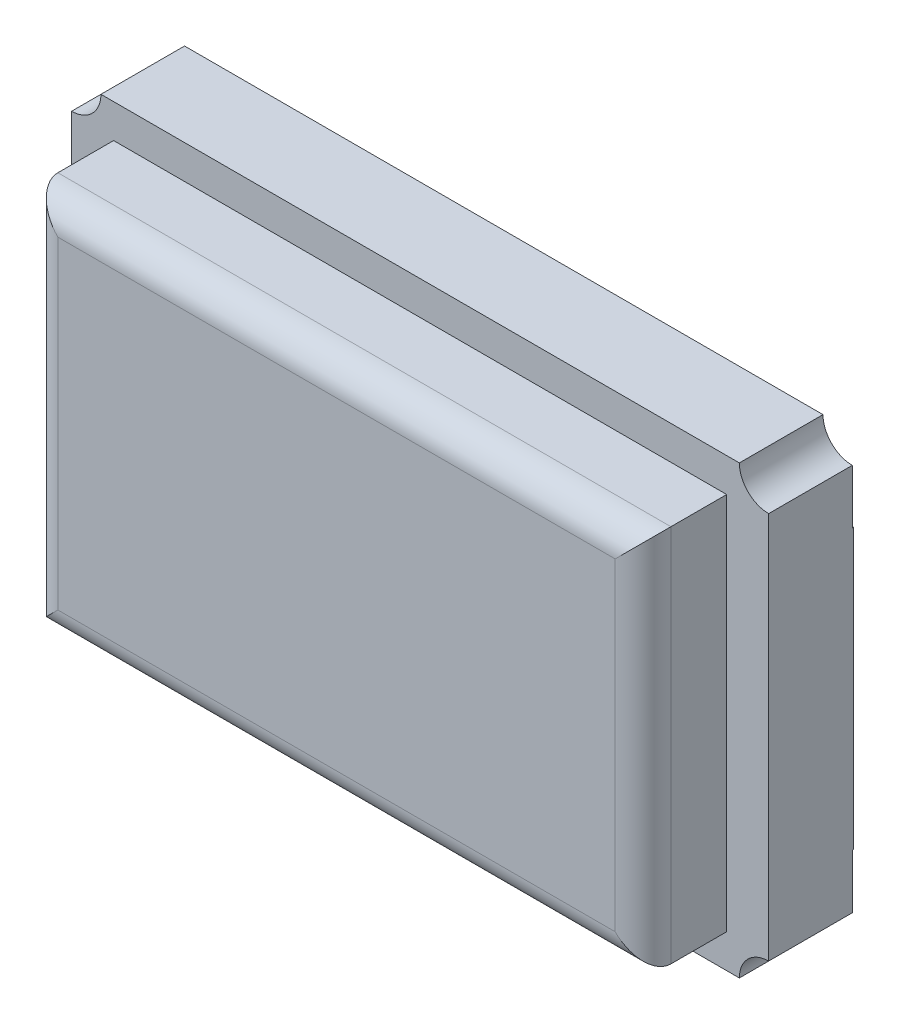
SolidWorks part; units mm, degrees
ref_plane "Front Plane" through (0, 0, 0) normal (0, 0, 1) x (1, 0, 0)
ref_plane "Top Plane" through (0, 0, 0) normal (0, 1, 0) x (1, 0, 0)
ref_plane "Right Plane" through (0, 0, 0) normal (1, 0, 0) x (0, 0, -1)
sketch "Sketch1" plane through (0, 0, 0) normal (0, 0, 1) x (1, 0, 0)
  line L0 (0, 1.6) -> (0, -1.6) construction
  line L1 (-2.2899, 1.6) -> (2.2899, 1.6)
  line L2 (-2.5, 1.3899) -> (-2.5, -1.3899)
  line L3 (-2.2899, -1.6) -> (2.2899, -1.6)
  line L4 (2.5, 1.3899) -> (2.5, -1.3899)
  line L5 (-2.3231, 1.4868) -> (2.3231, -1.4868) construction
  line L6 (-2.3231, -1.4868) -> (2.3231, 1.4868) construction
  line L7 (-2.5, 0) -> (2.5, 0) construction
  arc A0 (-2.5, 1.3899) -> (-2.2899, 1.6) centre (-2.5, 1.6) ccw
  arc A1 (2.5, 1.3899) -> (2.2899, 1.6) centre (2.5, 1.6) cw
  arc A2 (2.5, -1.3899) -> (2.2899, -1.6) centre (2.5, -1.6) ccw
  arc A3 (-2.5, -1.3899) -> (-2.2899, -1.6) centre (-2.5, -1.6) cw
  point P0 (0, 0)
extrude "Boss-Extrude1" add sketch "Sketch1" along normal blind 0.6
sketch "Sketch2" plane through (0, 0, 0.6) normal (0, 0, 1) x (1, 0, 0)
  line L1 (-2.1989, 1.3581) -> (2.1989, 1.3581)
  line L2 (-2.1989, 1.3581) -> (-2.1989, -1.3581)
  line L3 (-2.1989, -1.3581) -> (2.1989, -1.3581)
  line L4 (2.1989, 1.3581) -> (2.1989, -1.3581)
  line L5 (-2.1989, 1.3581) -> (2.1989, -1.3581) construction
  line L6 (-2.1989, -1.3581) -> (2.1989, 1.3581) construction
  point P0 (0, 0)
extrude "Boss-Extrude2" add sketch "Sketch2" along normal blind 0.6
sketch "Sketch3" plane through (0, 0, 0) normal (0, 0, -1) x (-1, 0, 0)
  line L0 (-2.5, -1.3899) -> (-2.5, 1.3899) construction
  line L1 (-2.5, 1) -> (-1.4, 1)
  line L2 (-2.5, 1) -> (-2.5, -1)
  line L3 (-2.5, -1) -> (-1.4, -1)
  line L4 (-1.4, 1) -> (-1.4, -1)
  line L5 (0, 1.6) -> (0, -1.6) construction
  line L6 (-2.2899, 1.6) -> (2.2899, 1.6) construction
  line L7 (2.2899, -1.6) -> (-2.2899, -1.6) construction
  line L8 (1.4, 1) -> (1.4, -1)
  line L9 (2.5, -1) -> (1.4, -1)
  line L10 (2.5, 1) -> (2.5, -1)
  line L11 (2.5, 1) -> (1.4, 1)
  point P12 (-1.4, 0)
  dimension "D1" = 2
  dimension "D2" = 1.1
extrude "Boss-Extrude3" add sketch "Sketch3" along normal blind 0.01
fillet "Fillet1" radius 0.2 4 edges at (0, -1.3581, 1.2) (-2.1989, 0, 1.2) (0, 1.3581, 1.2) (2.1989, 0, 1.2)
